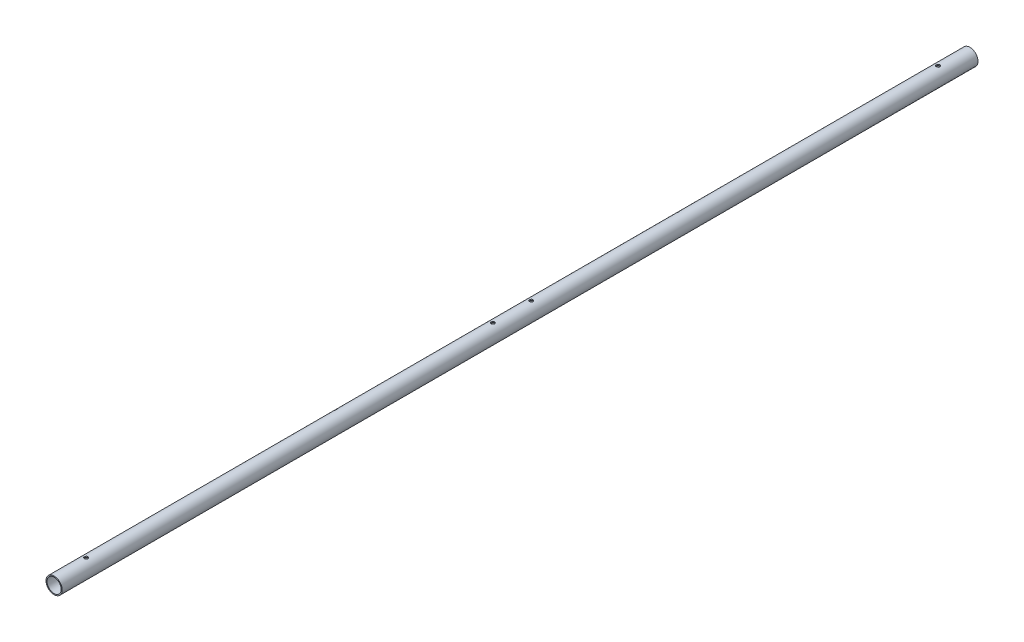
SolidWorks part; units mm, degrees
material "1060 Alloy"
ref_plane "Front Plane" through (0, 0, 0) normal (0, 0, 1) x (1, 0, 0)
ref_plane "Top Plane" through (0, 0, 0) normal (0, 1, 0) x (1, 0, 0)
ref_plane "Right Plane" through (0, 0, 0) normal (1, 0, 0) x (0, 0, -1)
sketch "Sketch1" plane through (0, 0, 0) normal (0, 0, 1) x (1, 0, 0)
  circle A0 centre (0, 0) radius 12.7
  circle A1 centre (0, 0) radius 11.1125
  dimension "D1" = 25.4
  dimension "D2" = 22.225
extrude "Boss-Extrude1" add sketch "Sketch1" along normal mid plane 1433.5092
ref_plane "Plane1" through (0, 12.7, 0) normal (0, 1, 0) x (1, 0, 0)
sketch "Sketch2" plane through (0, 12.7, 0) normal (0, 1, 0) x (1, 0, 0)
  line L0 (0, -30) -> (0, 30) construction
  dimension "D1" = 60
hole_wizard "M5 Clearance Hole1" positions "Sketch3" profile "Sketch4" hole size "M5" standard "AS" end condition through all
sketch "Sketch3" plane through (0, 12.7, 0) normal (0, 1, 0) x (1, 0, 0)
  point P0 (0, 30)
  point P3 (0, -30)
sketch "Sketch4" plane through (0, 12.7, -30) normal (1, 0, 0) x (0, 0, 1)
  line L0 (0, 0) -> (0, 25.4)
  line L1 (0, 25.4) -> (2.75, 25.4)
  line L2 (2.75, 25.4) -> (2.75, 0)
  line L5 (2.75, 0) -> (0, 0)
  line L11 (0, -6.35) -> (0, 107.95) construction
  dimension "Thru Hole Dia." = 5.5
  dimension "Thru Hole Depth" = 25.4
ref_plane "Plane2" through (-12.7, 0, 0) normal (-1, 0, 0) x (0, 0, 1)
sketch "Sketch5" plane through (0, 0, 0) normal (0, 1, 0) x (1, 0, 0)
  line L0 (0, -716.7546) -> (0, -666.7546) construction
  line L1 (-12.7, -716.7546) -> (12.7, -716.7546) construction
  dimension "D1" = 50
hole_wizard "M5 Clearance Hole2" positions "Sketch6" profile "Sketch7" hole size "M5" standard "AS"
sketch "Sketch6" plane through (0, 0, 0) normal (0, 1, 0) x (1, 0, 0)
  point P0 (0, -666.7546)
sketch "Sketch7" plane through (0, 0, 666.7546) normal (1, 0, 0) x (0, 0, -1)
  line L0 (0, 0) -> (0, 12.7)
  line L1 (0, 12.7) -> (2.75, 12.7)
  line L2 (2.75, 12.7) -> (2.75, 0)
  line L5 (2.75, 0) -> (0, 0)
  line L11 (0, -6.35) -> (0, 107.95) construction
  dimension "Thru Hole Dia." = 5.5
  dimension "Thru Hole Depth" = 12.7
mirror "Mirror1" about plane through (0, 0, 0) normal (0, 1, 0) of "M5 Clearance Hole2" second plane through (0, 0, 0) second plane normal (0, 0, 1)
ref_plane "Plane3" through (0, 0, 0) normal (0.5511, -0.8344, 0) x (-0.8344, -0.5511, 0)
sketch "Sketch8" plane through (0, 0, 0) normal (0.5511, -0.8344, 0) x (-0.8344, -0.5511, 0)
  line L0 (12.7, -716.7546) -> (12.7, 716.7546) construction
  circle A0 centre (1.717, 267.9176) radius 2.5
  circle A1 centre (3.764, 267.8963) radius 2.5 construction
  dimension "D1" = 267.9176
  dimension "D2" = 10.983
extrude "Cut-Extrude1" cut sketch "Sketch8" against normal up to surface and the other way up to surface
mirror "Mirror2" about plane through (0, 0, 0) normal (0, 0, 1) of "Cut-Extrude1"
equation "\"keelOutDiameter\"= 1in"
equation "\"keelInDiameter\"= \"keelOutDiameter\" - 0.125in"
equation "\"frontBoltClearance\"= 7.25mm"
equation "\"betweenBoltsDistance\"= 20mm"
equation "\"wingLength\"= 1.4m"
equation "\"frontTubeLength\"= \"wingLength\" / sin ( 34.95deg )"
equation "\"plateThickness\"= 5mm"
equation "\"crossBarOutDiameter\"= 1in"
equation "\"crossBarInDiameter\"= \"crossBarOutDiameter\" - 0.125in"
equation "\"D1@Sketch1\"=\"crossBarOutDiameter\""
equation "\"D2@Sketch1\"=\"crossBarInDiameter\""
equation "\"frontToCrossBar\"= 466mm"
equation "\"D1@Boss-Extrude1\"=2*(\"frontToCrossBar\"/ tan( 34.95))+10cm"
